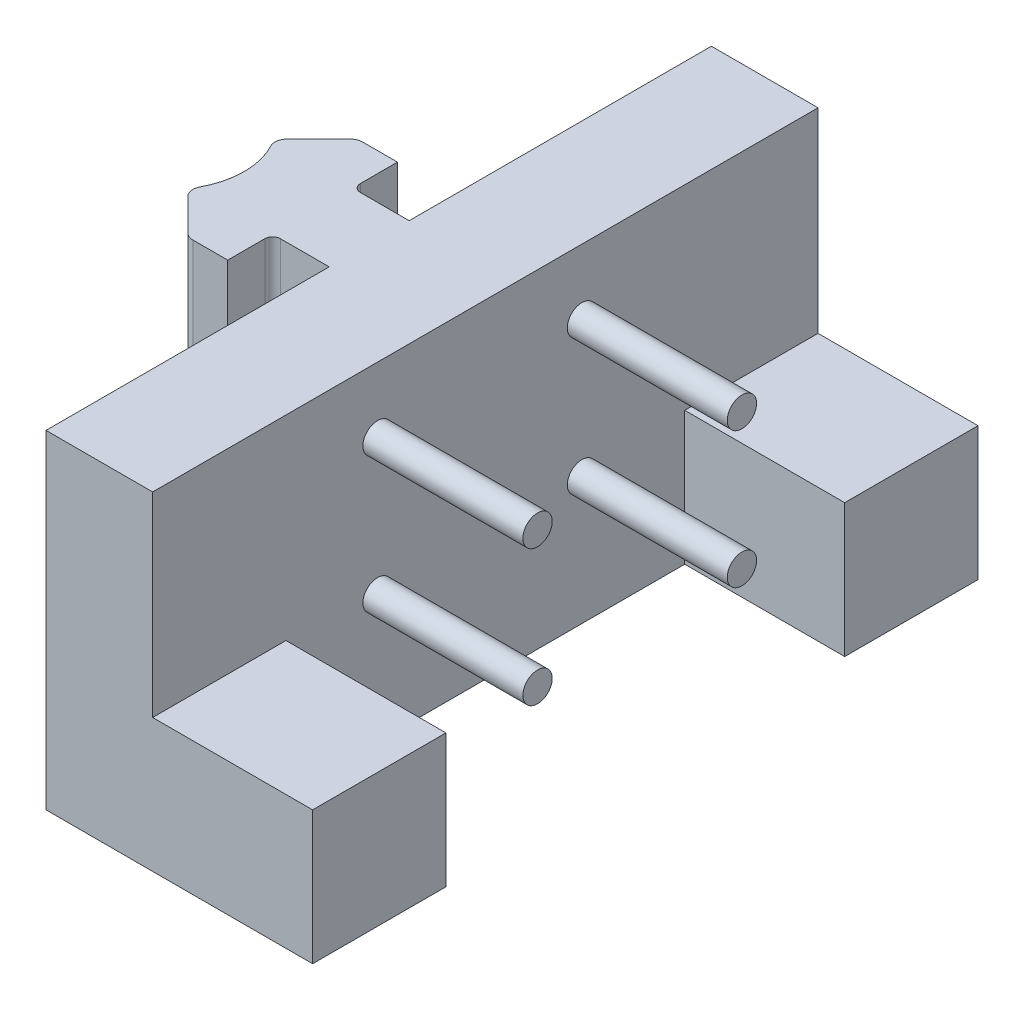
SolidWorks part; units mm, degrees
ref_plane "Front Plane" through (0, 0, 0) normal (0, 0, 1) x (1, 0, 0)
ref_plane "Top Plane" through (0, 0, 0) normal (0, 1, 0) x (1, 0, 0)
ref_plane "Right Plane" through (0, 0, 0) normal (1, 0, 0) x (0, 0, -1)
sketch "Sketch1" plane through (34.5685, 0, 0) normal (-1, 0, 0) x (0, 0, 1)
  line L1 (-320.8042, -67.476) -> (-245.9338, -67.476)
  line L2 (-320.8042, -67.476) -> (-320.8042, -104.456)
  line L3 (-320.8042, -104.456) -> (-245.9338, -104.456)
  line L4 (-245.9338, -67.476) -> (-245.9338, -104.456)
  line L6 (-300.0919, -97.476) -> (-289.0919, -97.476) construction
  line L7 (-300.0919, -67.476) -> (-289.0919, -67.476) construction
  point P0 (-282.742, -81.976)
  dimension "D1" = 6.98
extrude "Boss-Extrude1" add sketch "Sketch1" along normal blind 12
sketch "Sketch3" plane through (34.5685, 0, 0) normal (1, 0, 0) x (0, 0, -1)
  circle A0 centre (271.2419, -74.826) radius 1.651
  circle A1 centre (271.2419, -90.126) radius 1.651
  circle A2 centre (294.2419, -74.826) radius 1.651
  circle A3 centre (294.2419, -90.126) radius 1.651
  dimension "D1" = 3.302
extrude "Boss-Extrude2" add sketch "Sketch3" along normal up to surface (18 mm away)
sketch "Sketch4" plane through (34.5685, 0, 0) normal (1, 0, 0) x (0, 0, -1)
  line L0 (283.369, -67.476) -> (283.369, -104.456) construction
  line L1 (245.9338, -104.456) -> (260.9338, -104.456)
  line L2 (245.9338, -104.456) -> (245.9338, -89.456)
  line L3 (245.9338, -89.456) -> (260.9338, -89.456)
  line L4 (260.9338, -104.456) -> (260.9338, -89.456)
  line L5 (245.9338, -67.476) -> (320.8042, -67.476) construction
  line L6 (320.8042, -104.456) -> (245.9338, -104.456) construction
  line L7 (320.8042, -89.456) -> (305.8042, -89.456)
  line L8 (305.8042, -104.456) -> (305.8042, -89.456)
  line L9 (320.8042, -104.456) -> (305.8042, -104.456)
  line L10 (320.8042, -104.456) -> (320.8042, -89.456)
  dimension "D1" = 15
  dimension "D2" = 15
extrude "Boss-Extrude3" add sketch "Sketch4" along normal blind 18
sketch "Sketch5" plane through (0, -104.456, 0) normal (0, -1, 0) x (1, 0, 0)
  line L0 (22.5685, -283.369) -> (34.5685, -283.369) construction
  line L1 (22.5685, -320.8042) -> (22.5685, -245.9338) construction
  line L2 (34.5685, -305.8042) -> (34.5685, -260.9338) construction
  circle A0 centre (45.5185, -252.717) radius 4.075
  circle A2 centre (45.5185, -311.899) radius 4.25
  dimension "D1" = 8.15
extrude "Cut-Extrude1" cut sketch "Sketch5" against normal blind 12
sketch "Sketch7" plane through (0, -67.476, 0) normal (0, 1, 0) x (1, 0, 0)
  line L105 (8.4902, 282.7085) -> (8.4902, 281.8915)
  line L106 (20.8615, 286.8) -> (22.5685, 286.8)
  line L107 (22.5685, 245.9338) -> (22.5685, 320.8042) construction
  line L108 (20.8615, 277.8) -> (22.5685, 277.8)
  line L109 (22.5685, 277.8) -> (22.5685, 286.8)
  line L115 (17.077, 277.8) -> (20.8615, 277.8)
  line L116 (16.2, 272.75) -> (16.2, 276.923)
  line L117 (12.2808, 272.75) -> (16.2, 272.75)
  line L118 (7.7585, 276.6986) -> (11.3014, 273.1557)
  line L119 (8.2041, 282.3) -> (8.4902, 281.8915)
  line L120 (8.4902, 282.7085) -> (8.2041, 282.3)
  line L121 (11.3014, 291.4443) -> (7.7585, 287.9014)
  line L122 (16.2, 291.85) -> (12.2808, 291.85)
  line L123 (16.2, 287.677) -> (16.2, 291.85)
  line L124 (20.8615, 286.8) -> (17.077, 286.8)
  line L125 (17.077, 277.8) -> (20.8615, 277.8)
  line L126 (16.2, 272.75) -> (16.2, 276.923)
  line L127 (12.2808, 272.75) -> (16.2, 272.75)
  line L128 (7.7585, 276.6986) -> (11.3014, 273.1557)
  line L131 (11.3014, 291.4443) -> (7.7585, 287.9014)
  line L132 (16.2, 291.85) -> (12.2808, 291.85)
  line L133 (16.2, 287.677) -> (16.2, 291.85)
  line L134 (20.8615, 286.8) -> (17.077, 286.8)
  arc A115 (17.077, 277.8) -> (16.2, 276.923) centre (17.077, 276.923) ccw
  arc A116 (11.3014, 273.1557) -> (12.2808, 272.75) centre (12.2808, 274.135) ccw
  arc A117 (7.5136, 278.3256) -> (7.7585, 276.6986) centre (8.7378, 277.678) ccw
  arc A118 (7.5136, 278.3256) -> (8.4902, 281.8915) centre (0, 282.3) ccw
  arc A119 (8.4902, 282.7085) -> (7.5136, 286.2744) centre (0, 282.3) ccw
  arc A120 (7.7585, 287.9014) -> (7.5136, 286.2744) centre (8.7378, 286.922) ccw
  arc A121 (12.2808, 291.85) -> (11.3014, 291.4443) centre (12.2808, 290.465) ccw
  arc A122 (16.2, 287.677) -> (17.077, 286.8) centre (17.077, 287.677) ccw
  arc A123 (17.077, 277.8) -> (16.2, 276.923) centre (17.077, 276.923) ccw
  arc A124 (11.3014, 273.1557) -> (12.2808, 272.75) centre (12.2808, 274.135) ccw
  arc A125 (7.5136, 278.3256) -> (7.7585, 276.6986) centre (8.7378, 277.678) ccw
  arc A126 (7.5136, 278.3256) -> (8.4902, 281.8915) centre (0, 282.3) ccw
  arc A127 (8.4902, 282.7085) -> (7.5136, 286.2744) centre (0, 282.3) ccw
  arc A128 (7.7585, 287.9014) -> (7.5136, 286.2744) centre (8.7378, 286.922) ccw
  arc A129 (12.2808, 291.85) -> (11.3014, 291.4443) centre (12.2808, 290.465) ccw
  arc A130 (16.2, 287.677) -> (17.077, 286.8) centre (17.077, 287.677) ccw
  dimension "D1" = 0.5
extrude "Boss-Extrude4" add sketch "Sketch7" against normal up to surface (36.98 mm away) up to face at (49.5935, -104.456, -252.717)
